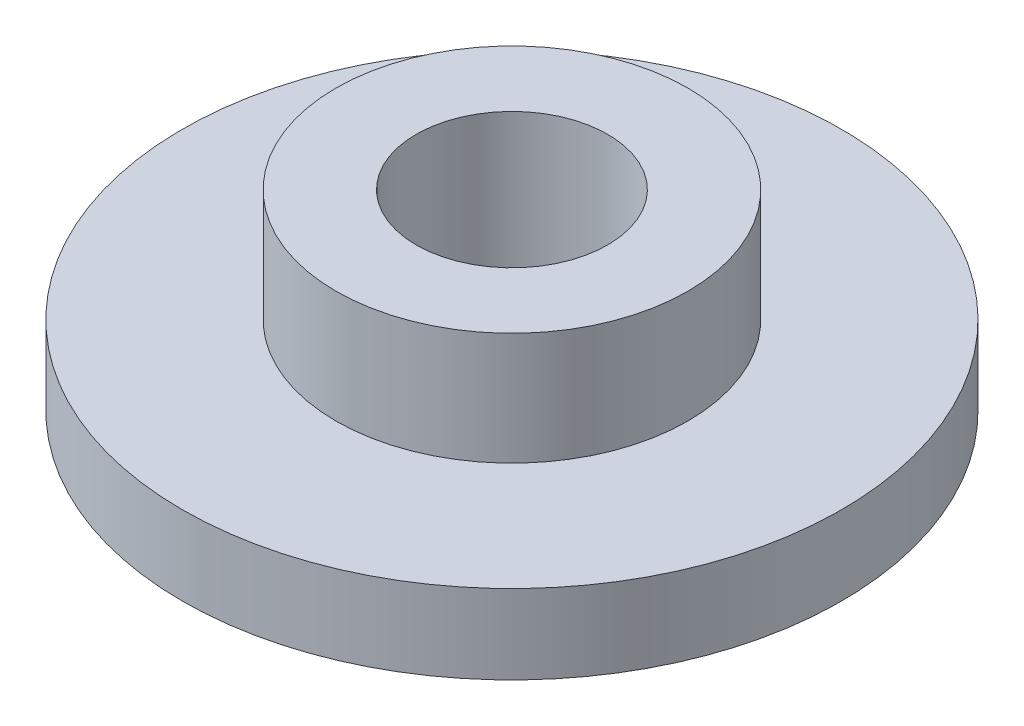
SolidWorks part; units mm, degrees
ref_plane "Front" through (0, 0, 0) normal (0, 0, 1) x (1, 0, 0)
ref_plane "Top" through (0, 0, 0) normal (0, 1, 0) x (1, 0, 0)
ref_plane "Right" through (0, 0, 0) normal (1, 0, 0) x (0, 0, -1)
sketch "Sketch1" plane through (0, 0, 0) normal (0, 0, 1) x (1, 0, 0)
  line L0 (-13.7594, 0) -> (-4, 0)
  line L4 (-4, 0) -> (-4, 8)
  line L5 (-4, 8) -> (-7.3464, 8)
  line L6 (-7.3464, 3.3045) -> (-7.3464, 8)
  line L7 (-13.7594, 3.3045) -> (-7.3464, 3.3045)
  line L8 (-13.7594, 3.3045) -> (-13.7594, 0)
  line L11 (-13.7594, 0) -> (-50000, 0) construction
  line L13 (0, 0) -> (0, -50000) construction
  dimension "D2" = 8
revolve "Revolve1" add sketch "Sketch1" angle 360 about L13
